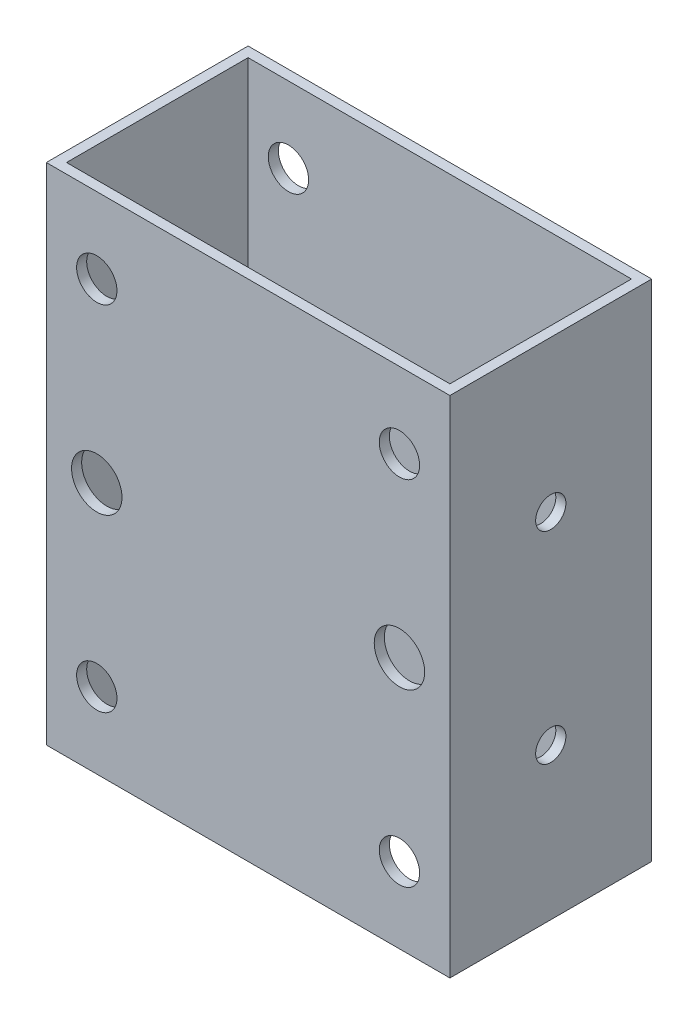
SolidWorks part; units mm, degrees
material "1060 Alloy"
ref_plane "Front" through (0, 0, 0) normal (0, 0, 1) x (1, 0, 0)
ref_plane "Top" through (0, 0, 0) normal (0, 1, 0) x (1, 0, 0)
ref_plane "Right" through (0, 0, 0) normal (1, 0, 0) x (0, 0, -1)
sketch "Sketch1" plane through (0, 0, 0) normal (0, 1, 0) x (1, 0, 0)
  line L0 (2, 2) -> (2, 38)
  line L1 (0, 0) -> (80, 0)
  line L2 (0, 0) -> (0, 40)
  line L3 (0, 40) -> (80, 40)
  line L4 (80, 0) -> (80, 40)
  line L5 (2, 38) -> (78, 38)
  line L6 (78, 2) -> (78, 38)
  line L7 (2, 2) -> (78, 2)
  dimension "D2" = 80
  dimension "D3" = 40
  dimension "D1" = 2
extrude "Boss-Extrude1" add sketch "Sketch1" along normal blind 100
sketch "Sketch2" plane through (0, 0, 0) normal (0, 0, 1) x (1, 0, 0)
  line L0 (40, 100) -> (40, 0) construction
  line L1 (0, 100) -> (80, 100) construction
  line L2 (0, 0) -> (80, 0) construction
  line L4 (0, 100) -> (0, 0) construction
  circle A0 centre (70, 15) radius 4
  circle A1 centre (70, 85) radius 4
  circle A2 centre (10, 15) radius 4
  circle A3 centre (10, 50) radius 5
  circle A4 centre (10, 85) radius 4
  circle A5 centre (70, 50) radius 5
  dimension "D3" = 2
  dimension "D4" = 60
  dimension "D5" = 70
  dimension "D6" = 8
  dimension "D9" = 35
  dimension "D8" = 10
  dimension "D1" = 10
  dimension "D2" = 2
  dimension "D7" = 15
extrude "Cut-Extrude1" cut sketch "Sketch2" against normal up to surface (40 mm away) up to face at (40, 50, -40)
sketch "Sketch3" plane through (0, 0, 0) normal (-1, 0, 0) x (0, 0, 1)
  line L0 (-40, 0) -> (0, 0) construction
  line L2 (-40, 100) -> (-40, 0) construction
  line L3 (-40, 50) -> (49960, 50) construction
  line L4 (0, 100) -> (0, 0) construction
  circle A0 centre (-20, 30) radius 3
  circle A1 centre (-20, 70) radius 3
  point P10 (-40, 50)
  point P13 (0, 50)
  dimension "D1" = 6
  dimension "D2" = 20
  dimension "D3" = 30
extrude "Cut-Extrude2" cut sketch "Sketch3" against normal up to surface (80 mm away) up to face at (80, 50, -20)
